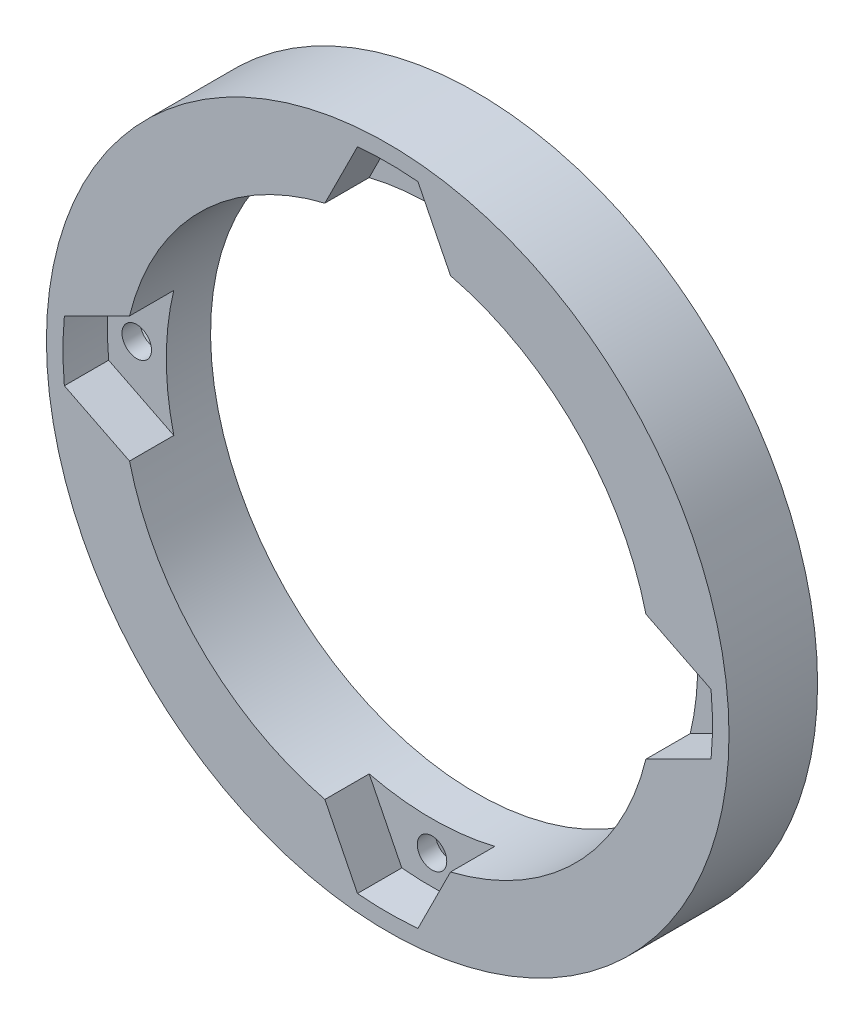
SolidWorks part; units mm, degrees
ref_plane "Front Plane" through (0, 0, 0) normal (0, 0, 1) x (1, 0, 0)
ref_plane "Top Plane" through (0, 0, 0) normal (0, 1, 0) x (1, 0, 0)
ref_plane "Right Plane" through (0, 0, 0) normal (1, 0, 0) x (0, 0, -1)
sketch "Sketch2" plane through (0, 0, 0) normal (0, 0, 1) x (1, 0, 0)
  circle A0 centre (0, 0) radius 73.406
  circle A1 centre (0, 0) radius 57.15
extrude "Boss-Extrude1" add sketch "Sketch2" along normal blind 19.05
sketch "Sketch7" plane through (0, 0, 19.05) normal (0, 0, 1) x (1, 0, 0)
  line L3 (-69.5468, 6.5016) -> (-55.5302, 13.5099)
  line L4 (-69.5468, -6.5016) -> (-55.5302, -13.5099)
  line L5 (6.5016, 69.5468) -> (13.5099, 55.5302)
  line L6 (-6.5016, 69.5468) -> (-13.5099, 55.5302)
  line L7 (69.5468, -6.5016) -> (55.5302, -13.5099)
  line L8 (69.5468, 6.5016) -> (55.5302, 13.5099)
  line L9 (-6.5016, -69.5468) -> (-13.5099, -55.5302)
  line L10 (6.5016, -69.5468) -> (13.5099, -55.5302)
  arc A0 (-13.5099, -55.5302) -> (13.5099, -55.5302) centre (0, 0) ccw
  arc A1 (-6.5016, -69.5468) -> (6.5016, -69.5468) centre (0, 0) ccw
  arc A2 (-69.5468, 6.5016) -> (-69.5468, -6.5016) centre (0, 0) ccw
  arc A3 (-55.5302, 13.5099) -> (-55.5302, -13.5099) centre (0, 0) ccw
  arc A4 (13.5099, 55.5302) -> (-13.5099, 55.5302) centre (0, 0) ccw
  arc A5 (6.5016, 69.5468) -> (-6.5016, 69.5468) centre (0, 0) ccw
  arc A6 (69.5468, -6.5016) -> (69.5468, 6.5016) centre (0, 0) ccw
  arc A7 (55.5302, -13.5099) -> (55.5302, 13.5099) centre (0, 0) ccw
  point P23 (0, 0)
  dimension "D1" = 4
extrude "Cut-Extrude5" cut sketch "Sketch7" against normal blind 9.525
sketch "Sketch9" plane through (0, 0, 9.525) normal (0, 0, 1) x (1, 0, 0)
  circle A2 centre (-63.5, 0) radius 3.175
  circle A3 centre (0, 63.5) radius 3.175
  circle A4 centre (63.5, 0) radius 3.175
  circle A5 centre (0, -63.5) radius 3.175
  point P11 (0, 0)
  dimension "D1" = 4
extrude "Cut-Extrude6" cut sketch "Sketch9" against normal blind 9.525
sketch "Sketch10" plane through (0, 0, 0) normal (0, 0, -1) x (-1, 0, 0)
  line L0 (-6.3058, 63.5) -> (-3.1529, 58.039)
  line L1 (-63.5, -6.3058) -> (-58.039, -3.1529)
  line L2 (-58.039, -3.1529) -> (-58.039, 3.1529)
  line L3 (-58.039, 3.1529) -> (-63.5, 6.3058)
  line L4 (-63.5, 6.3058) -> (-68.961, 3.1529)
  line L5 (-68.961, 3.1529) -> (-68.961, -3.1529)
  line L6 (-68.961, -3.1529) -> (-63.5, -6.3058)
  line L7 (-3.1529, 58.039) -> (3.1529, 58.039)
  line L8 (3.1529, 58.039) -> (6.3058, 63.5)
  line L9 (6.3058, 63.5) -> (3.1529, 68.961)
  line L10 (3.1529, 68.961) -> (-3.1529, 68.961)
  line L11 (-3.1529, 68.961) -> (-6.3058, 63.5)
  line L12 (63.5, 6.3058) -> (58.039, 3.1529)
  line L13 (58.039, 3.1529) -> (58.039, -3.1529)
  line L14 (58.039, -3.1529) -> (63.5, -6.3058)
  line L15 (63.5, -6.3058) -> (68.961, -3.1529)
  line L16 (68.961, -3.1529) -> (68.961, 3.1529)
  line L17 (68.961, 3.1529) -> (63.5, 6.3058)
  line L18 (6.3058, -63.5) -> (3.1529, -58.039)
  line L19 (3.1529, -58.039) -> (-3.1529, -58.039)
  line L20 (-3.1529, -58.039) -> (-6.3058, -63.5)
  line L21 (-6.3058, -63.5) -> (-3.1529, -68.961)
  line L22 (-3.1529, -68.961) -> (3.1529, -68.961)
  line L23 (3.1529, -68.961) -> (6.3058, -63.5)
  circle A0 centre (-63.5, 0) radius 5.461 construction
  point P30 (0, 0)
  dimension "D1" = 10.922
  dimension "D2" = 4
extrude "Cut-Extrude7" cut sketch "Sketch10" against normal blind 5.588
